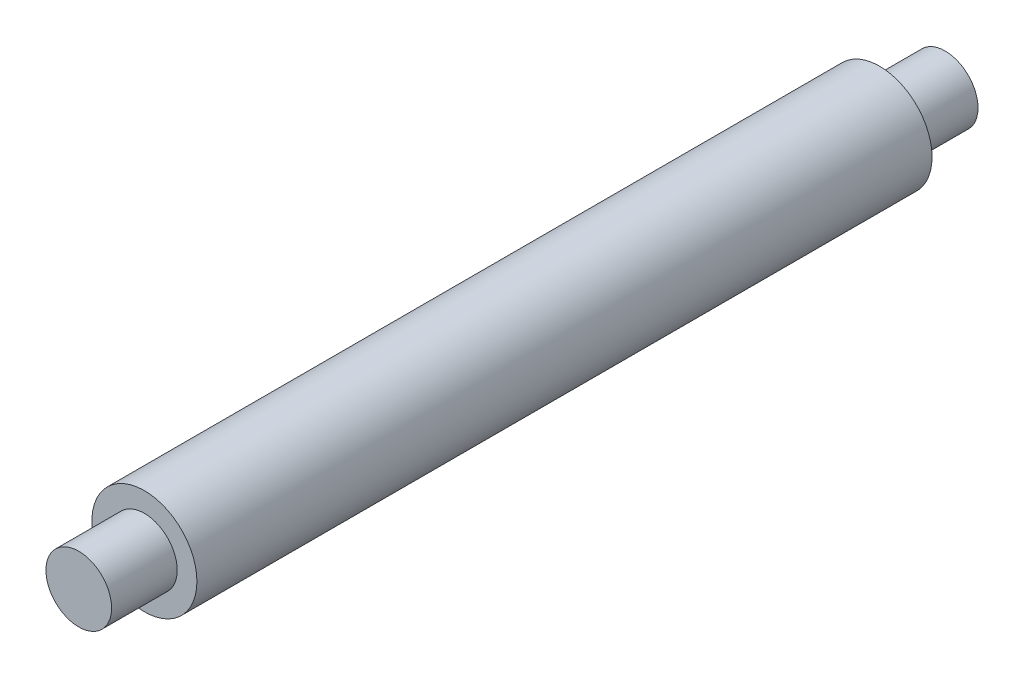
SolidWorks part; units mm, degrees
ref_plane "Alzado" through (0, 0, 0) normal (0, 0, 1) x (1, 0, 0)
ref_plane "Planta" through (0, 0, 0) normal (0, 1, 0) x (1, 0, 0)
ref_plane "Vista lateral" through (0, 0, 0) normal (1, 0, 0) x (0, 0, -1)
sketch "Croquis1" plane through (0, 0, 0) normal (0, 0, 1) x (1, 0, 0)
  circle A0 centre (0, 0) radius 4
  dimension "D1" = 8
extrude "Saliente-Extruir1" add sketch "Croquis1" along normal blind 56
sketch "Croquis2" plane through (0, 0, 56) normal (0, 0, 1) x (1, 0, 0)
  circle A0 centre (0, 0) radius 2.5
  dimension "D1" = 5
extrude "Saliente-Extruir2" add sketch "Croquis2" along normal blind 5
sketch "Croquis3" plane through (0, 0, 0) normal (0, 0, -1) x (-1, 0, 0)
  circle A0 centre (0, 0) radius 2.5
  dimension "D1" = 5
extrude "Saliente-Extruir3" add sketch "Croquis3" along normal blind 5
